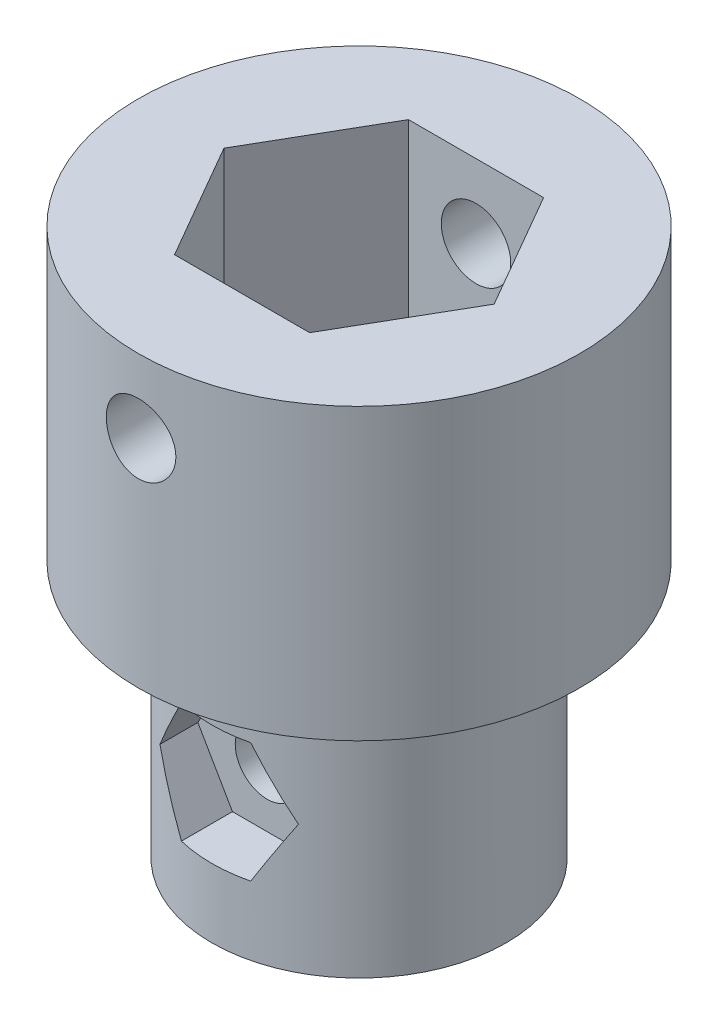
SolidWorks part; units mm, degrees
ref_plane "Front Plane" through (0, 0, 0) normal (0, 0, 1) x (1, 0, 0)
ref_plane "Top Plane" through (0, 0, 0) normal (0, 1, 0) x (1, 0, 0)
ref_plane "Right Plane" through (0, 0, 0) normal (1, 0, 0) x (0, 0, -1)
sketch "Sketch1" plane through (0, 0, 0) normal (0, 1, 0) x (1, 0, 0)
  circle A0 centre (0, 0) radius 7.62
  dimension "D1" = 15.24
extrude "Boss-Extrude1" add sketch "Sketch1" along normal blind 10
sketch "Sketch2" plane through (0, 10, 0) normal (0, 1, 0) x (1, 0, 0)
  line L1 (-2.3317, 4.0386) -> (-4.6634, 0)
  line L2 (-4.6634, 0) -> (-2.3317, -4.0386)
  line L3 (-2.3317, -4.0386) -> (2.3317, -4.0386)
  line L4 (2.3317, -4.0386) -> (4.6634, 0)
  line L5 (4.6634, 0) -> (2.3317, 4.0386)
  line L6 (2.3317, 4.0386) -> (-2.3317, 4.0386)
  circle A0 centre (0, 0) radius 4.0386 construction
  dimension "D1" = 8.0772
extrude "Cut-Extrude1" cut sketch "Sketch2" against normal blind 7.62
sketch "Sketch4" plane through (0, 2.38, 0) normal (0, 1, 0) x (1, 0, 0)
  circle A0 centre (0, 0) radius 2.75
  dimension "D1" = 5.5
extrude "Cut-Extrude2" cut sketch "Sketch4" against normal blind 9.5
sketch "Sketch5" plane through (0, 0, 0) normal (0, -1, 0) x (-1, 0, 0)
  circle A0 centre (0, 0) radius 5.08
  dimension "D1" = 10.16
extrude "Boss-Extrude2" add sketch "Sketch5" along normal blind 8.89
sketch "Sketch6" plane through (0, -8.89, 0) normal (0, -1, 0) x (-1, 0, 0)
  circle A0 centre (0, 0) radius 2.0892
  dimension "D1" = 4.1783
extrude "Cut-Extrude3" cut sketch "Sketch6" against normal up to next
sketch "Sketch7" plane through (0, 0, 0) normal (0, 0, 1) x (1, 0, 0)
  line L0 (-5.08, -8.89) -> (5.08, -8.89) construction
  circle A0 centre (0, -4.445) radius 1.1
  dimension "D1" = 2.2
  dimension "D2" = 4.445
extrude "Cut-Extrude4" cut sketch "Sketch7" against normal blind 8.89 and the other way blind 8.89
sketch "Sketch8" plane through (0, 0, 0) normal (0, 0, 1) x (1, 0, 0)
  line L0 (7.62, 10) -> (-7.62, 10) construction
  circle A0 centre (0, 7.46) radius 1.2
  dimension "D1" = 2.4
  dimension "D2" = 2.54
extrude "Cut-Extrude5" cut sketch "Sketch8" against normal blind 8.89 and the other way blind 8.89
ref_plane "Plane1" through (0, 0, 5.08) normal (0, 0, 1) x (1, 0, 0)
sketch "Sketch9" plane through (0, 0, 5.08) normal (0, 0, 1) x (1, 0, 0)
  line L0 (-5.08, -8.89) -> (5.08, -8.89) construction
  line L1 (1.1952, -2.3749) -> (-1.1952, -2.3749)
  line L2 (-1.1952, -2.3749) -> (-2.3903, -4.445)
  line L3 (-2.3903, -4.445) -> (-1.1952, -6.5151)
  line L4 (-1.1952, -6.5151) -> (1.1952, -6.5151)
  line L5 (1.1952, -6.5151) -> (2.3903, -4.445)
  line L6 (2.3903, -4.445) -> (1.1952, -2.3749)
  circle A0 centre (0, -4.445) radius 2.0701 construction
  dimension "D1" = 4.1402
extrude "Cut-Extrude6" cut sketch "Sketch9" against normal blind 1.905
